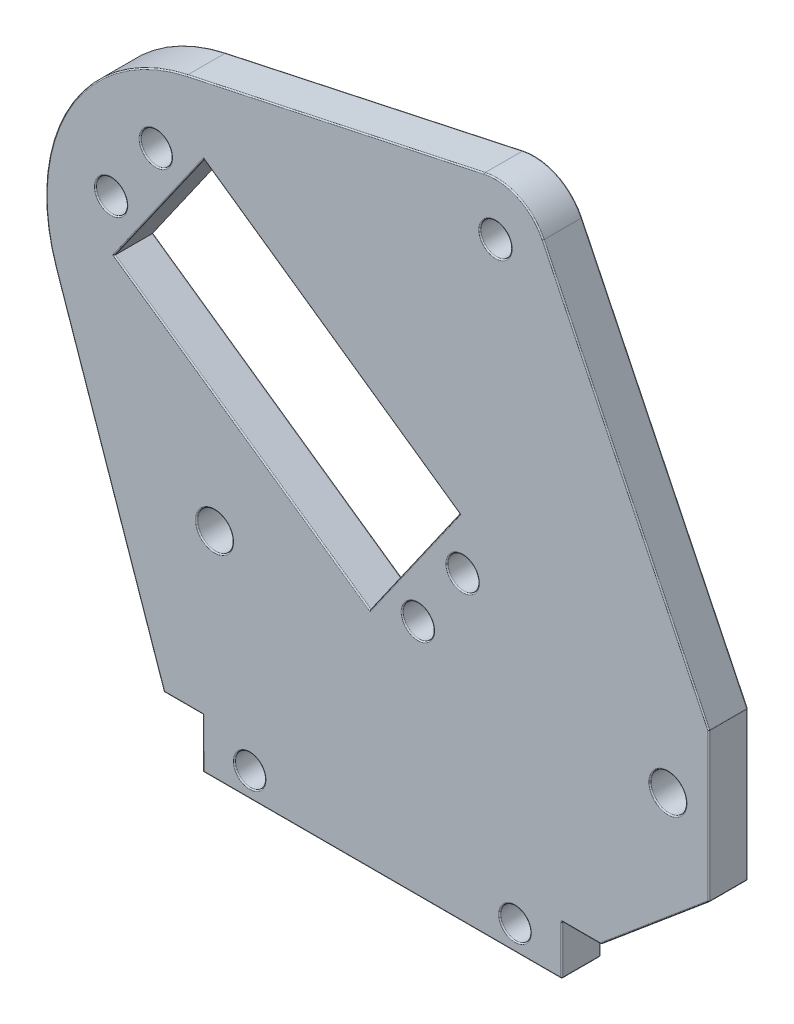
SolidWorks part; units mm, degrees
ref_plane "Front Plane" through (0, 0, 0) normal (0, 0, 1) x (1, 0, 0)
ref_plane "Top Plane" through (0, 0, 0) normal (0, 1, 0) x (1, 0, 0)
ref_plane "Right Plane" through (0, 0, 0) normal (1, 0, 0) x (0, 0, -1)
sketch "Sketch2" plane through (0, 0, 0) normal (0, 0, 1) x (1, 0, 0)
  line L0 (-23, 0) -> (-23, 10) construction
  line L1 (-23, 10) -> (-28, 10) construction
  line L2 (-28, 10) -> (-41.8438, 50.1182) construction
  line L3 (-25.0297, 79.9436) -> (13.0723, 88.1382) construction
  line L4 (41.85, 40.6215) -> (20.6106, 84.4605) construction
  line L5 (41.85, 21.6215) -> (41.85, 40.6215) construction
  line L6 (28, 10) -> (41.85, 21.6215) construction
  line L7 (23, 10) -> (28, 10) construction
  line L9 (23, 0) -> (23, 10) construction
  line L10 (-23, 0) -> (-23, 10)
  line L11 (-23, 10) -> (-28, 10)
  line L12 (-28, 10) -> (-41.8438, 50.1182)
  line L13 (-25.0297, 79.9436) -> (13.0723, 88.1382)
  line L14 (41.85, 40.6215) -> (20.6106, 84.4605)
  line L15 (41.85, 21.6215) -> (41.85, 40.6215)
  line L16 (28, 10) -> (41.85, 21.6215)
  line L17 (23, 10) -> (28, 10)
  line L19 (23, 0) -> (23, 10)
  line L20 (0, 0) -> (0, 10) construction
  line L21 (-22.8805, 71.6507) -> (-34.3521, 55.2676)
  line L22 (-22.8805, 71.6507) -> (9.8855, 48.7076)
  line L23 (-34.3521, 55.2676) -> (-1.586, 32.3246)
  line L24 (9.8855, 48.7076) -> (-1.586, 32.3246)
  line L25 (4.1498, 40.5161) -> (-28.6163, 63.4592) construction
  line L26 (-22.8805, 71.6507) -> (-34.3521, 55.2676) construction
  line L30 (-28.6163, 63.4592) -> (-33.5312, 66.9006) construction
  line L31 (-33.5312, 66.9006) -> (-28.6163, 63.4592) construction
  line L32 (-33.5312, 66.9006) -> (-27.7955, 75.0921) construction
  line L33 (-28.6163, 63.4592) -> (-22.8805, 71.6507) construction
  line L34 (-27.7955, 75.0921) -> (-22.8805, 71.6507) construction
  line L39 (-33.5312, 66.9006) -> (-28.6163, 63.4592) construction
  line L40 (-33.5312, 66.9006) -> (-39.267, 58.7091) construction
  line L41 (-28.6163, 63.4592) -> (-34.3521, 55.2676) construction
  line L42 (-39.267, 58.7091) -> (-34.3521, 55.2676) construction
  line L43 (-30.6633, 70.9964) -> (-25.7484, 67.5549) construction
  line L44 (-36.3991, 62.8049) -> (-31.4842, 59.3634) construction
  line L45 (-17.969, 43.7961) -> (-6.4975, 60.1792) construction
  line L46 (-23, 0) -> (23, 0)
  arc A0 (-25.0297, 79.9436) -> (-41.8438, 50.1182) centre (-20.22, 57.58) ccw construction
  arc A1 (20.6106, 84.4605) -> (13.0723, 88.1382) centre (14.5, 81.5) ccw construction
  arc A2 (-25.0297, 79.9436) -> (-41.8438, 50.1182) centre (-20.22, 57.58) ccw
  arc A3 (20.6106, 84.4605) -> (13.0723, 88.1382) centre (14.5, 81.5) ccw
  circle A6 centre (-29.025, 69.8492) radius 2
  circle A7 centre (-34.7608, 61.6577) radius 2
  circle A8 centre (10.2943, 42.3176) radius 2
  circle A9 centre (4.5585, 34.126) radius 2
  circle A10 centre (14.5, 81.5) radius 2
  circle A11 centre (36.6, 31.1215) radius 2.3
  circle A12 centre (17, 6.8) radius 1.95
  circle A13 centre (-17, 6.8) radius 1.95
  circle A14 centre (-21.5, 31.1215) radius 2.3
  point P2 (-17, 6.8)
  point P4 (17, 6.8)
  point P8 (36.6, 31.1215)
  point P9 (-21.5, 31.1215)
  point P13 (41.85, 31.1215)
  point P15 (14.5, 81.5)
  point P26 (-20.22, 57.58)
  dimension "D9" = 4
  dimension "D10" = 4
  dimension "D2" = 4.6
  dimension "D6" = 3.9
  dimension "D1" = 5.25
  dimension "D3" = 21.5
  dimension "D4" = 40
  dimension "D5" = 20
  dimension "D7" = 10.25
  dimension "D8" = 6
  dimension "D11" = 6
sketch "Sketch3" plane through (0, 0, 0) normal (0, 0, 1) x (1, 0, 0)
extrude "Boss-Extrude2" add sketch "Sketch2" against normal blind 5
sketch "Sketch4" plane through (0, 0, 0) normal (0, 0, 1) x (1, 0, 0)
  line L0 (23, 0) -> (23, 10) construction
  line L1 (23, 10) -> (28, 10) construction
  line L3 (-23, 0) -> (23, 0)
  line L4 (-23, 0) -> (-23, 3.65)
  line L5 (-23, 3.65) -> (23, 3.65)
  line L6 (23, 0) -> (23, 3.65)
  point P0 (23, 3.65)
  dimension "D1" = 6.35
extrude "Cut-Extrude1" cut sketch "Sketch4" against normal through all
fillet "Fillet1" radius 0.15 57 edges at (23, 6.825, 0) (23, 10, -2.5) (23, 6.825, -5) (23, 3.65, -2.5) (0, 3.65, 0) (0, 3.65, -5) (-23, 3.65, -2.5) (-19.2, 31.1215, 0) (-19.2, 31.1215, -5) (-15.05, 6.8, 0) (-15.05, 6.8, -5) (18.95, 6.8, 0) (18.95, 6.8, -5) (38.9, 31.1215, 0) (38.9, 31.1215, -5) (16.5, 81.5, 0) (16.5, 81.5, -5) (6.5585, 34.126, 0) (6.5585, 34.126, -5) (8.2943, 42.3176, 0) (8.2943, 42.3176, -5) (-36.7608, 61.6577, 0) (-36.7608, 61.6577, -5) (-27.025, 69.8492, 0) (-27.025, 69.8492, -5) (-6.4975, 60.1792, 0) (-28.6163, 63.4592, 0) (-17.969, 43.7961, 0) (4.1498, 40.5161, 0) (-6.4975, 60.1792, -5) (-28.6163, 63.4592, -5) (-17.969, 43.7961, -5) (4.1498, 40.5161, -5) (25.5, 10, 0) (34.925, 15.8108, 0) (41.85, 31.1215, 0) (31.2303, 62.541, 0) (17.4772, 87.6025, 0) (-5.9787, 84.0409, 0) (-40.1467, 68.8136, 0) (-34.9219, 30.0591, 0) (-25.5, 10, 0) (-23, 6.825, 0) (25.5, 10, -5) (34.925, 15.8108, -5) (41.85, 31.1215, -5) (31.2303, 62.541, -5) (17.4772, 87.6025, -5) (-5.9787, 84.0409, -5) (-40.1467, 68.8136, -5) (-34.9219, 30.0591, -5) (-25.5, 10, -5) (-23, 6.825, -5) (28, 10, -2.5) (41.85, 21.6215, -2.5) (41.85, 40.6215, -2.5) (-28, 10, -2.5)
